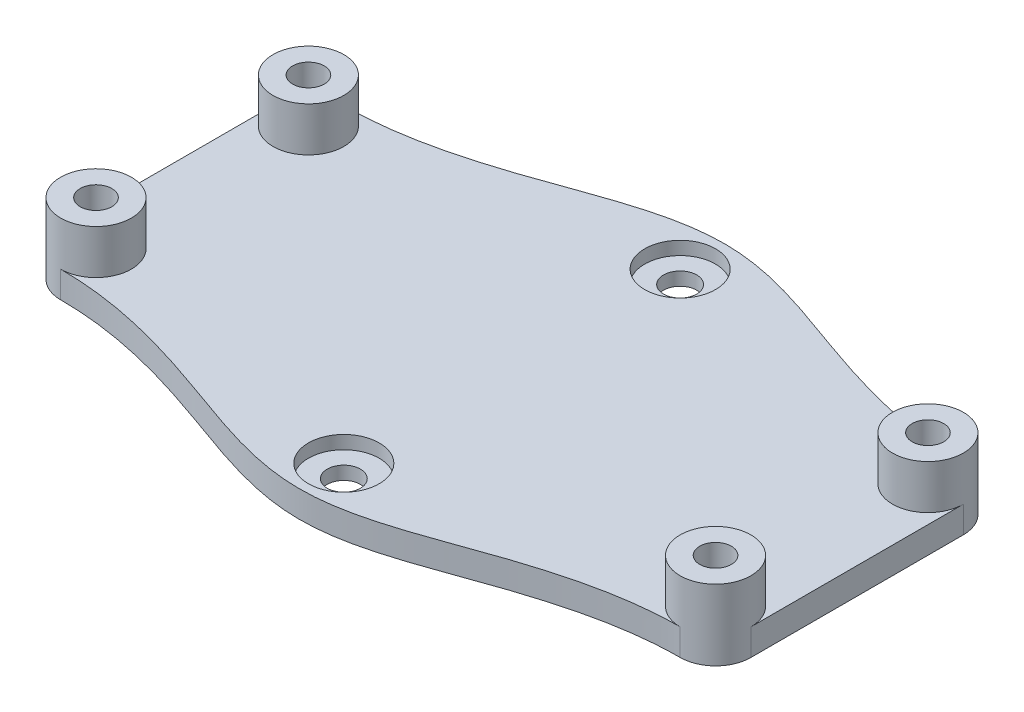
SolidWorks part; units mm, degrees
ref_plane "Front Plane" through (0, 0, 0) normal (0, 0, 1) x (1, 0, 0)
ref_plane "Top Plane" through (0, 0, 0) normal (0, 1, 0) x (1, 0, 0)
ref_plane "Right Plane" through (0, 0, 0) normal (1, 0, 0) x (0, 0, -1)
sketch "Sketch11" plane through (0, 0, 0) normal (0, 1, 0) x (1, 0, 0)
  line L0 (-36.2519, -5.9898) -> (33.7481, -5.9898) construction
  line L1 (-36.2519, 6.0102) -> (33.7481, 6.0102) construction
  line L2 (-36.2519, 6.0102) -> (-36.2519, -17.9898) construction
  line L3 (-36.2519, -17.9898) -> (33.7481, -17.9898) construction
  line L4 (33.7481, 6.0102) -> (33.7481, -17.9898) construction
  line L5 (-1.2519, -24.9898) -> (-1.2519, 13.0102) construction
  line L6 (37.7481, 6.0102) -> (37.7481, -17.9898)
  line L7 (-40.2519, 6.0102) -> (-40.2519, -17.9898)
  line L8 (-36.2519, 10.0102) -> (-1.2519, 17.0102) construction
  line L9 (-1.2519, 17.0102) -> (33.7481, 10.0102) construction
  line L10 (-36.2519, -21.9898) -> (-1.2519, -28.9898) construction
  line L11 (-1.2519, -28.9898) -> (33.7481, -21.9898) construction
  line L12 (-1.2519, 17.0102) -> (-1.2519, 18.0102) construction
  line L13 (-1.2519, -28.9898) -> (-1.2519, -29.9898) construction
  line L14 (-31.5125, -21.9898) -> (-40.9913, -21.9898) construction
  line L15 (38.4934, -21.9898) -> (29.0028, -21.9898) construction
  line L16 (3.4089, -29.9898) -> (-5.9126, -29.9898) construction
  line L17 (38.4875, 10.0102) -> (29.0087, 10.0102) construction
  line L18 (-31.5066, 10.0102) -> (-40.9972, 10.0102) construction
  line L19 (3.4089, 18.0102) -> (-5.9126, 18.0102) construction
  circle A0 centre (-36.2519, 6.0102) radius 4 construction
  circle A1 centre (-36.2519, -17.9898) radius 4 construction
  circle A2 centre (33.7481, 6.0102) radius 4 construction
  circle A3 centre (33.7481, -17.9898) radius 4 construction
  arc A4 (-40.2519, 6.0102) -> (-36.2519, 10.0102) centre (-36.2519, 6.0102) cw
  arc A5 (37.7481, 6.0102) -> (33.7481, 10.0102) centre (33.7481, 6.0102) ccw
  arc A6 (33.7481, -21.9898) -> (37.7481, -17.9898) centre (33.7481, -17.9898) ccw
  arc A7 (-40.2519, -17.9898) -> (-36.2519, -21.9898) centre (-36.2519, -17.9898) ccw
  circle A8 centre (-1.2519, 13.0102) radius 4 construction
  circle A9 centre (-1.2519, -24.9898) radius 4 construction
  spline S0 degree 3 poles (-36.2519, 10.0102) (-30.3202, 10.0102) (-19.2471, 12.8935) (-7.0778, 18.0326) (4.5741, 18.0326) (16.7401, 12.8935) (27.8239, 10.0102) (33.7481, 10.0102) knots 0 0 0 0 0.24845 0.474845 0.525155 0.75155 1 1 1 1
  spline S1 degree 3 poles (-36.2519, -21.9898) (-30.3276, -21.9898) (-19.2439, -24.8732) (-7.0778, -30.0122) (4.5741, -30.0122) (16.7433, -24.8732) (27.8165, -21.9898) (33.7481, -21.9898) knots 0 0 0 0 0.24845 0.474845 0.525155 0.75155 1 1 1 1
  point P23 (-1.2519, -5.9898)
  point P24 (-1.2519, -5.9898)
  dimension "D1" = 24
  dimension "D2" = 70
extrude "Boss-Extrude3" add sketch "Sketch11" against normal blind 3
sketch "Sketch13" plane through (0, 0, 0) normal (0, 1, 0) x (1, 0, 0)
  circle A0 centre (-36.2519, -17.9898) radius 4
  circle A1 centre (-36.2519, 6.0102) radius 4
  circle A2 centre (33.7481, 6.0102) radius 4
  circle A3 centre (33.7481, -17.9898) radius 4
  circle A4 centre (-36.2519, 6.0102) radius 1.7859
  circle A5 centre (-36.2519, -17.9898) radius 1.7859
  circle A6 centre (33.7481, -17.9898) radius 1.7859
  circle A7 centre (33.7481, 6.0102) radius 1.7859
  point P12 (34.0226, -17.9898)
  point P15 (0, 0)
  point P16 (33.4535, 6.0102)
  point P18 (0, 0)
  point P21 (-36.2519, -17.8819)
  point P22 (0, 0)
  point P23 (0, 0)
  point P24 (33.9219, 6.0102)
extrude "Boss-Extrude4" add sketch "Sketch13" along normal blind 5
sketch "Sketch14" plane through (0, 0, 0) normal (0, 1, 0) x (1, 0, 0)
  circle A0 centre (-1.2519, 13.0102) radius 4
  circle A1 centre (-1.2519, -24.9898) radius 4
extrude "Cut-Extrude8" cut sketch "Sketch14" against normal blind 1.5
sketch "Sketch15" plane through (0, 0, 0) normal (0, 1, 0) x (1, 0, 0)
  circle A0 centre (-1.2519, -24.9898) radius 1.875
  circle A1 centre (-1.2519, 13.0102) radius 1.875
extrude "Cut-Extrude9" cut sketch "Sketch15" against normal through all
